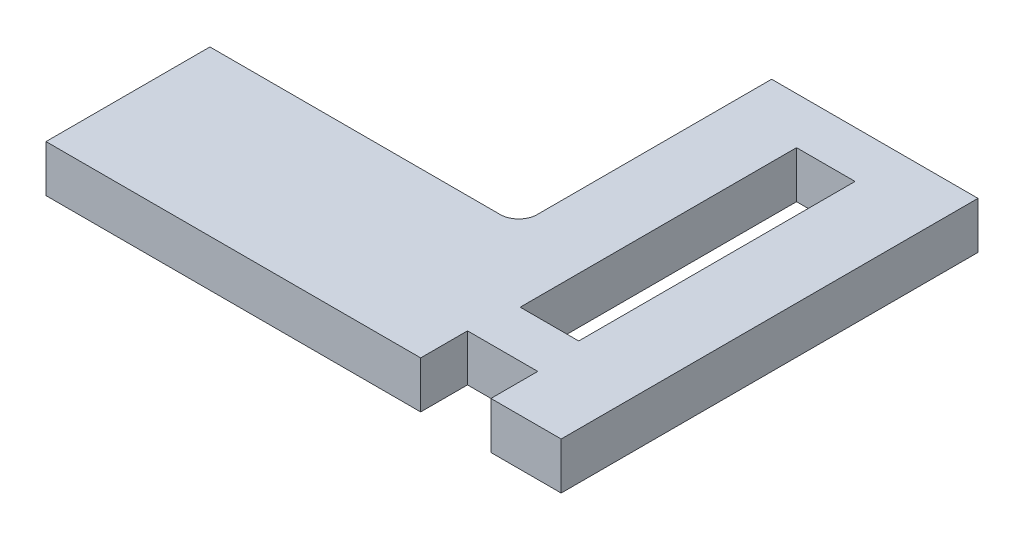
SolidWorks part; units mm, degrees
ref_plane "Front Plane" through (0, 0, 0) normal (0, 0, 1) x (1, 0, 0)
ref_plane "Top Plane" through (0, 0, 0) normal (0, 1, 0) x (1, 0, 0)
ref_plane "Right Plane" through (0, 0, 0) normal (1, 0, 0) x (0, 0, -1)
sketch "Sketch1" plane through (0, 0, 0) normal (0, 1, 0) x (1, 0, 0)
  line L0 (0, 0) -> (0, 88.9)
  line L1 (0, 88.9) -> (157.48, 88.9)
  line L2 (167.48, 98.9) -> (167.48, 226.06)
  line L3 (167.48, 226.06) -> (279.4, 226.06)
  line L4 (279.4, 226.06) -> (279.4, 0)
  line L5 (279.4, 0) -> (241.3, 0)
  line L6 (241.3, 0) -> (241.3, 25.4)
  line L7 (241.3, 25.4) -> (203.2, 25.4)
  line L8 (203.2, 25.4) -> (203.2, 0)
  line L9 (203.2, 0) -> (0, 0)
  line L11 (206.3786, 50.8) -> (238.1214, 50.8)
  line L12 (206.3786, 50.8) -> (206.3786, 200.66)
  line L13 (206.3786, 200.66) -> (238.1214, 200.66)
  line L14 (238.1214, 50.8) -> (238.1214, 200.66)
  arc A0 (157.48, 88.9) -> (167.48, 98.9) centre (157.48, 98.9) ccw
  point P17 (282.7769, 0)
  point P18 (306.7175, 0)
  point P19 (222.2212, 0)
  dimension "D1" = 10
  dimension "D2" = 88.9
  dimension "D3" = 203.2
  dimension "D4" = 25.4
  dimension "D5" = 38.1
  dimension "D6" = 38.1
  dimension "D7" = 157.48
  dimension "D8" = 226.06
  dimension "D9" = 149.86
  dimension "D10" = 25.4
  dimension "D11" = 25.5981
  dimension "D12" = 25.5981
extrude "Boss-Extrude1" add sketch "Sketch1" along normal blind 25.4 contours L1 A0 L2 L3 L4 L5 L6 L7 L8 L9 L0 | L12 L13 L14 L11
